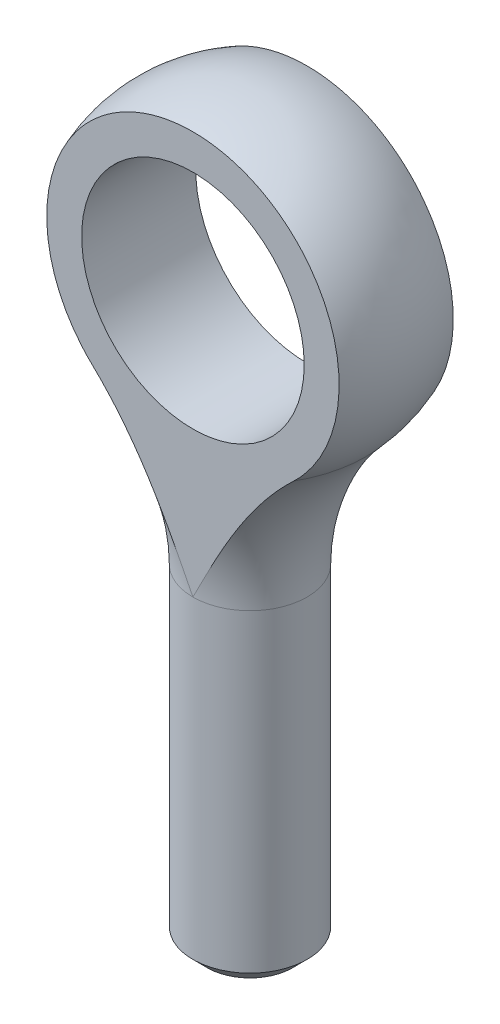
SolidWorks part; units mm, degrees
ref_plane "Front" through (0, 0, 0) normal (0, 0, 1) x (1, 0, 0)
ref_plane "Top" through (0, 0, 0) normal (0, 1, 0) x (1, 0, 0)
ref_plane "Right" through (0, 0, 0) normal (1, 0, 0) x (0, 0, -1)
sketch "Sketch1" plane through (0, 0, 0) normal (0, 0, 1) x (1, 0, 0)
  line L0 (0, 0) -> (0, -36.5125)
  line L1 (0, -36.5125) -> (6.35, -36.5125)
  line L2 (6.35, -36.5125) -> (6.35, 0)
  line L3 (6.35, 0) -> (0, 0)
  line L5 (0, 46.0375) -> (0, 0) construction
  line L6 (0, 46.0375) -> (17.4625, 46.0375) construction
  line L7 (17.4625, 46.0375) -> (17.4625, 28.575) construction
  line L8 (-6.35, -36.5125) -> (-6.35, 0) construction
  arc A0 (12.8745, 16.7773) -> (0, 46.0375) centre (0, 28.575) ccw construction
  circle A1 centre (0, 28.575) radius 6.35 construction
  circle A2 centre (0, 28.575) radius 16.6687 construction
  circle A3 centre (0, 28.575) radius 17.4625 construction
  arc A4 (6.35, 0) -> (12.8745, 16.7773) centre (31.183, 0) cw construction
  dimension "A" = 12.7
  dimension "B" = 34.925
  dimension "D1" = 34.925
  dimension "Thread Dia" = 12.7
  dimension "D2" = 82.55
revolve "Revolve1" add sketch "Sketch1" angle 360 about L5
chamfer "Chamfer2" distance 1.5875 angle 45 1 edges at (-6.35, -36.5125, 0)
sketch "Sketch4" plane through (0, 0, 0) normal (0, 0, 1) x (1, 0, 0)
  line L0 (6.35, 0) -> (0, 0) construction
  line L2 (0, 46.0375) -> (0, 0) construction
  line L3 (6.35, 0) -> (0, 0)
  line L5 (0, 46.0375) -> (0, 0)
  line L6 (0, 46.0375) -> (0, 48.5775) construction
  arc A0 (12.8745, 16.7773) -> (0, 46.0375) centre (0, 28.575) ccw construction
  arc A1 (12.8745, 16.7773) -> (0, 46.0375) centre (0, 28.575) ccw
  arc A2 (12.8745, 16.7773) -> (6.35, 0) centre (31.183, 0) ccw construction
  arc A3 (12.8745, 16.7773) -> (6.35, 0) centre (31.183, 0) ccw
  dimension "D1" = 2.54
revolve "Revolve2" add sketch "Sketch4" angle 360 about L6
sketch "Sketch5" plane through (0, 0, 0) normal (1, 0, 0) x (0, 0, -1)
  line L0 (6.35, 46.0375) -> (17.4625, 46.0375)
  line L1 (-6.35, 46.0375) -> (6.35, 46.0375) construction
  line L2 (-6.35, 46.0375) -> (-6.35, 0)
  line L3 (-6.35, 0) -> (6.35, 0) construction
  line L4 (6.35, 46.0375) -> (6.35, 0)
  line L5 (17.4625, 46.0375) -> (17.4625, 0)
  line L6 (17.4625, 0) -> (6.35, 0)
  line L7 (-6.35, 0) -> (-17.4625, 0)
  line L8 (-17.4625, 0) -> (-17.4625, 46.0375)
  line L9 (-17.4625, 46.0375) -> (-6.35, 46.0375)
  line L13 (0, 0) -> (0, 3.0162) construction
  arc A0 (12.8745, 16.7773) -> (-12.8745, 16.7773) centre (0, 28.575) ccw construction
  dimension "D1" = 12.7
extrude "Cut-Extrude1" cut sketch "Sketch5" against normal through all and the other way through all
sketch "Sketch6" plane through (0, 0, 0) normal (0, 0, 1) x (1, 0, 0)
  circle A1 centre (0, 28.575) radius 12.3825
extrude "Cut-Extrude2" cut sketch "Sketch6" against normal through all and the other way through all
ref_plane "Plane1" through (0, 0, 0) normal (0, 1, 0) x (1, 0, 0)
ref_plane "Plane2" through (0, -34.925, 0) normal (0, 1, 0) x (1, 0, 0)
scale "Scale1" scale about centroid uniform scaling yes scale factor 0.75
scale "Scale2" scale about centroid uniform scaling yes scale factor 0.666667
equation "\"D1@Sketch1\"= 1.375'."
equation "\"D1@Sketch5\"=\"Thread Dia@Sketch1\""
